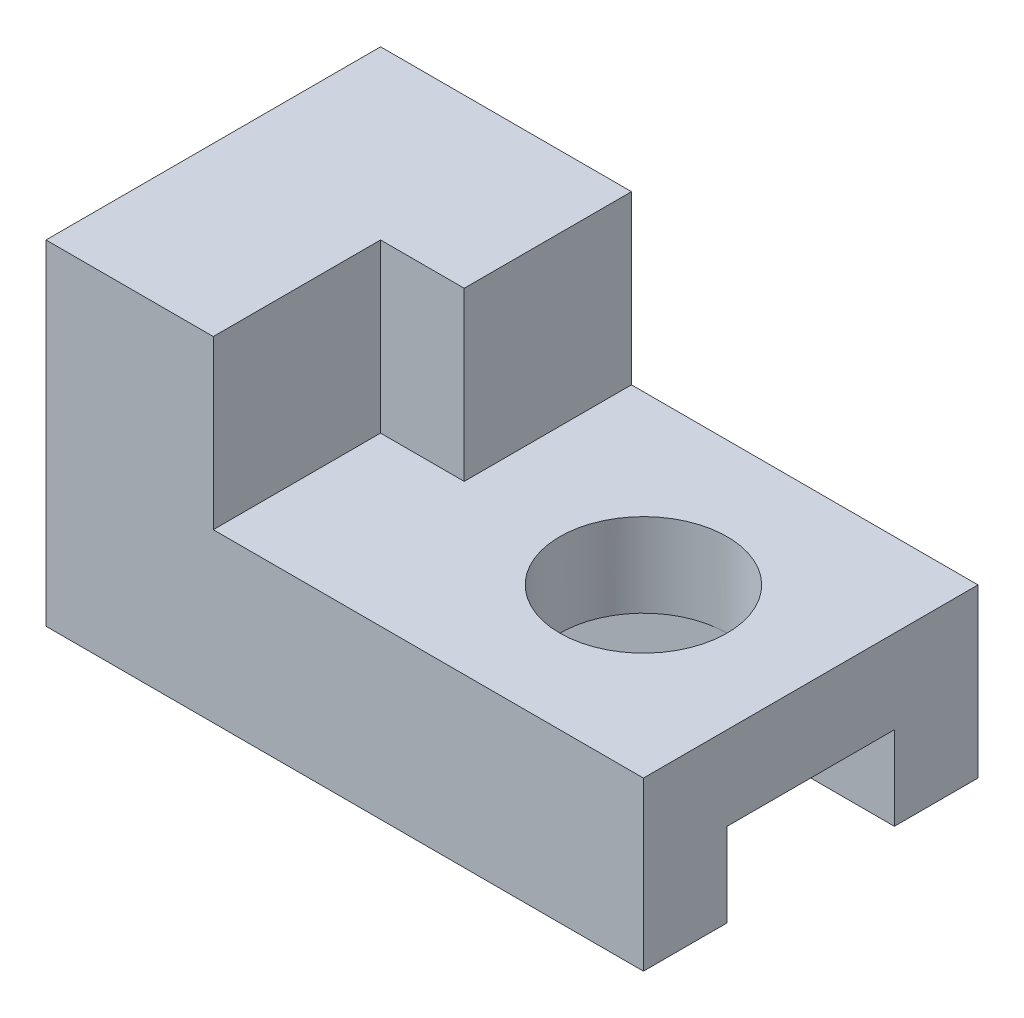
SolidWorks part; units mm, degrees
ref_plane "Front Plane" through (0, 0, 0) normal (0, 0, 1) x (1, 0, 0)
ref_plane "Top Plane" through (0, 0, 0) normal (0, 1, 0) x (1, 0, 0)
ref_plane "Right Plane" through (0, 0, 0) normal (1, 0, 0) x (0, 0, -1)
sketch "Sketch1" plane through (0, 0, 0) normal (1, 0, 0) x (0, 0, -1)
  line L0 (0, 0) -> (0, 14)
  line L1 (0, 14) -> (28, 14)
  line L2 (28, 14) -> (28, 0)
  line L3 (28, 0) -> (21, 0)
  line L4 (21, 0) -> (21, 7)
  line L5 (21, 7) -> (7, 7)
  line L6 (7, 7) -> (7, 0)
  line L7 (7, 0) -> (0, 0)
  line L8 (14, 14) -> (14, 7) construction
  dimension "D1" = 14
  dimension "D2" = 28
  dimension "D3" = 7
  dimension "D4" = 14
extrude "Boss-Extrude1" add sketch "Sketch1" along normal mid plane 50
sketch "Sketch2" plane through (0, 14, 0) normal (0, 1, 0) x (1, 0, 0)
  line L0 (-25, 14) -> (25, 14) construction
  line L1 (-25, 28) -> (-25, 0) construction
  line L2 (25, 28) -> (25, 0) construction
  circle A0 centre (11, 14) radius 7
  dimension "D2" = 14
  dimension "D1" = 14
extrude "Cut-Extrude1" cut sketch "Sketch2" against normal up to next
sketch "Sketch3" plane through (0, 14, 0) normal (0, 1, 0) x (1, 0, 0)
  line L0 (-4, 28) -> (-4, 14)
  line L1 (-4, 14) -> (-11, 14)
  line L2 (-11, 14) -> (-11, 0)
  line L4 (-25, 28) -> (-25, 0)
  line L5 (-25, 0) -> (25, 0)
  line L6 (25, 0) -> (25, 28)
  line L7 (25, 28) -> (-25, 28)
  line L8 (-25, 28) -> (-25, 0)
  line L9 (-25, 0) -> (25, 0)
  line L10 (25, 0) -> (25, 28)
  line L11 (25, 28) -> (-25, 28)
  line M6 (-25, 28) -> (-25, 0)
  line M7 (-25, 0) -> (25, 0)
  line M9 (25, 28) -> (-25, 28)
  dimension "D2" = 21
  dimension "D3" = 14
  dimension "D4" = 14
  dimension "D1" = 0
extrude "Boss-Extrude2" add sketch "Sketch3" along normal blind 14 contours L2 L1 L0 M9 M6 M7
